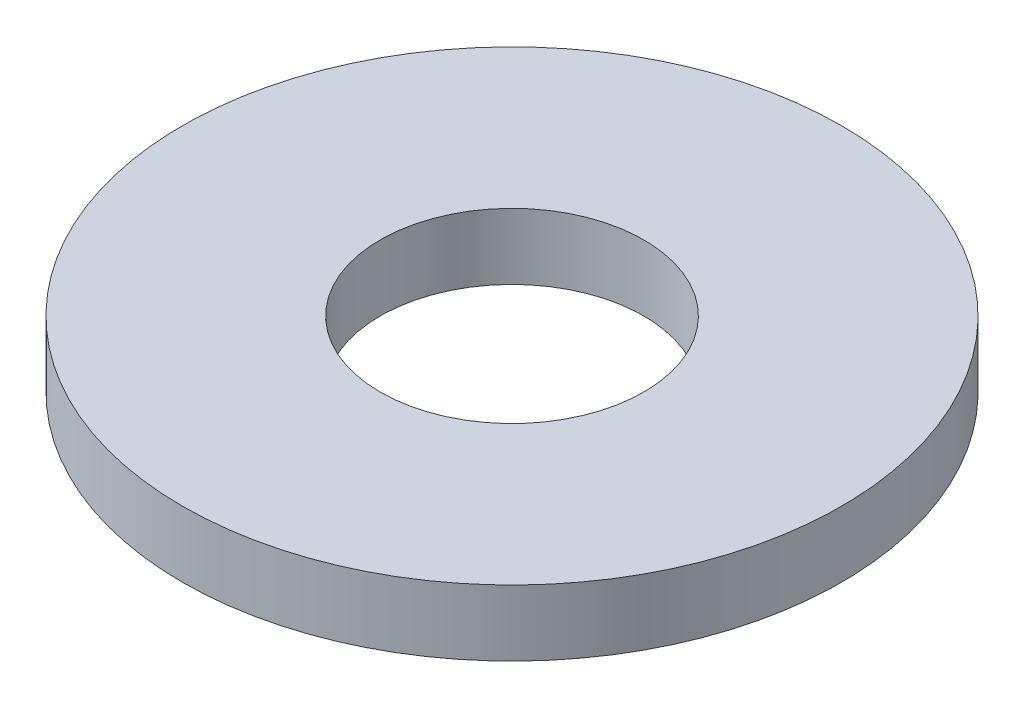
SolidWorks part; units mm, degrees
material "Aluminum Bronze"
ref_plane "Front Plane" through (0, 0, 0) normal (0, 0, 1) x (1, 0, 0)
ref_plane "Top Plane" through (0, 0, 0) normal (0, 1, 0) x (1, 0, 0)
ref_plane "Right Plane" through (0, 0, 0) normal (1, 0, 0) x (0, 0, -1)
sketch "Sketch1" plane through (0, 0, 0) normal (0, 1, 0) x (1, 0, 0)
  circle A0 centre (0, 0) radius 3.175
  circle A1 centre (0, 0) radius 7.9375
  dimension "D1" = 6.35
  dimension "D2" = 15.875
extrude "Boss-Extrude1" add sketch "Sketch1" along normal blind 1.5875
